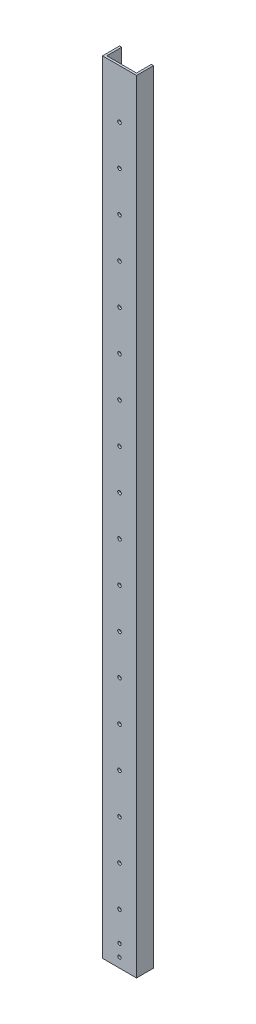
SolidWorks part; units mm, degrees
ref_plane "Front" through (0, 0, 0) normal (0, 0, 1) x (1, 0, 0)
ref_plane "Top" through (0, 0, 0) normal (0, 1, 0) x (1, 0, 0)
ref_plane "Right" through (0, 0, 0) normal (1, 0, 0) x (0, 0, -1)
sketch "Sketch1" plane through (0, 0, 0) normal (0, 1, 0) x (1, 0, 0)
  line L0 (3.175, 3.175) -> (3.175, 25.4)
  line L1 (0, 0) -> (50.8, 0)
  line L2 (0, 0) -> (0, 25.4)
  line L4 (50.8, 0) -> (50.8, 25.4)
  line L5 (3.175, 3.175) -> (47.625, 3.175)
  line L6 (47.625, 3.175) -> (47.625, 25.4)
  line L7 (0, 25.4) -> (3.175, 25.4)
  line L8 (50.8, 25.4) -> (47.625, 25.4)
  dimension "D1" = 25.4
  dimension "D2" = 50.8
  dimension "D3" = 3.175
extrude "Boss-Extrude1" add sketch "Sketch1" along normal blind 1168.4
sketch "Sketch2" plane through (0, 0, 0) normal (0, 0, 1) x (1, 0, 0)
  line L0 (25.4, 0) -> (25.4, 76.2) construction
  line L1 (0, 0) -> (50.8, 0) construction
  circle A0 centre (25.4, 76.2) radius 2.667
  circle A1 centre (25.4, 136.144) radius 2.667
  circle A2 centre (25.4, 196.088) radius 2.667
  circle A3 centre (25.4, 256.032) radius 2.667
  circle A4 centre (25.4, 315.976) radius 2.667
  circle A5 centre (25.4, 375.92) radius 2.667
  circle A6 centre (25.4, 435.864) radius 2.667
  circle A7 centre (25.4, 495.808) radius 2.667
  circle A8 centre (25.4, 555.752) radius 2.667
  circle A9 centre (25.4, 615.696) radius 2.667
  circle A10 centre (25.4, 675.64) radius 2.667
  circle A11 centre (25.4, 735.584) radius 2.667
  circle A12 centre (25.4, 795.528) radius 2.667
  circle A13 centre (25.4, 855.472) radius 2.667
  circle A14 centre (25.4, 915.416) radius 2.667
  circle A15 centre (25.4, 975.36) radius 2.667
  circle A16 centre (25.4, 1035.304) radius 2.667
  circle A17 centre (25.4, 1095.248) radius 2.667
  dimension "D2" = 5.334
  dimension "D1" = 76.2
  dimension "D3" = 18
extrude "Cut-Extrude1" cut sketch "Sketch2" against normal up to next
ref_plane "Mid_Plane" through (25.4, 0, 0) normal (1, 0, 0) x (0, 0, -1)
sketch "Sketch3" plane through (0, 0, 0) normal (0, 0, 1) x (1, 0, 0)
  circle A1 centre (25.4, 32.131) radius 2.5527
  circle A3 centre (25.4, 14.2875) radius 2.5527
extrude "Cut-Extrude2" cut sketch "Sketch3" against normal up to next
